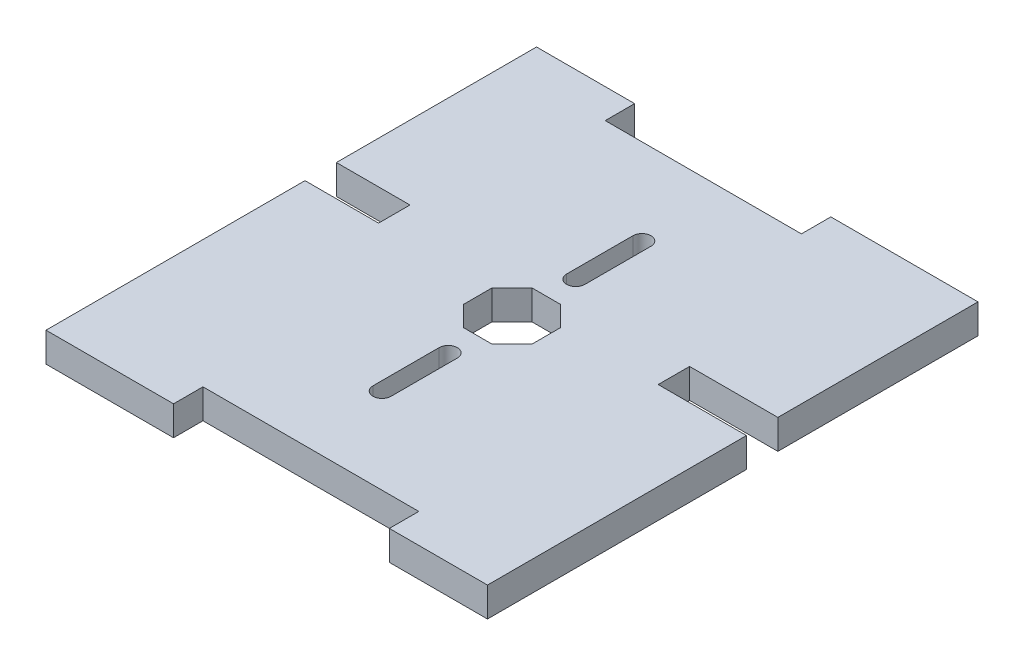
SolidWorks part; units mm, degrees
ref_plane "Front Plane" through (0, 0, 0) normal (0, 0, 1) x (1, 0, 0)
ref_plane "Top Plane" through (0, 0, 0) normal (0, 1, 0) x (1, 0, 0)
ref_plane "Right Plane" through (0, 0, 0) normal (1, 0, 0) x (0, 0, -1)
sketch "Sketch1" plane through (0, 0, 0) normal (0, 1, 0) x (1, 0, 0)
  line L1 (0, 0) -> (45, 0)
  line L2 (0, 0) -> (0, 50)
  line L3 (0, 50) -> (45, 50)
  line L4 (45, 0) -> (45, 50)
  dimension "D1" = 50
  dimension "D2" = 45
extrude "Boss-Extrude1" add sketch "Sketch1" along normal blind 3
sketch "Sketch2" plane through (0, 3, 0) normal (0, 1, 0) x (1, 0, 0)
  line L0 (45, 50) -> (0, 50) construction
  line L1 (10, 50) -> (30, 50)
  line L2 (10, 50) -> (10, 47)
  line L3 (10, 47) -> (30, 47)
  line L4 (30, 50) -> (30, 47)
  line L5 (0, 50) -> (0, 0) construction
  line L6 (0, 0) -> (45, 0) construction
  line L7 (13, 0) -> (35, 0)
  line L8 (13, 0) -> (13, 3)
  line L9 (13, 3) -> (35, 3)
  line L10 (35, 0) -> (35, 3)
  line L11 (45, 0) -> (45, 50) construction
  line L12 (0, 29.5) -> (7.5, 29.5)
  line L13 (0, 29.5) -> (0, 26.5)
  line L14 (0, 26.5) -> (7.5, 26.5)
  line L15 (7.5, 29.5) -> (7.5, 26.5)
  line L16 (45, 29.5) -> (36, 29.5)
  line L17 (45, 29.5) -> (45, 26.5)
  line L18 (45, 26.5) -> (36, 26.5)
  line L19 (36, 29.5) -> (36, 26.5)
  line L20 (22.5, 31.5) -> (22.5, 38.25) construction
  line L21 (21.0503, 21.5) -> (23.9497, 21.5)
  line L22 (23.9497, 21.5) -> (26, 23.5503)
  line L23 (26, 23.5503) -> (26, 26.4497)
  line L24 (26, 26.4497) -> (23.9497, 28.5)
  line L25 (23.9497, 28.5) -> (21.0503, 28.5)
  line L26 (21.0503, 28.5) -> (19, 26.4497)
  line L27 (19, 26.4497) -> (19, 23.5503)
  line L28 (19, 23.5503) -> (21.0503, 21.5)
  line L29 (21.575, 31.5) -> (21.575, 38.25)
  line L30 (23.425, 31.5) -> (23.425, 38.25)
  line L31 (22.5, 18.5) -> (22.5, 11.75) construction
  line L32 (23.425, 18.5) -> (23.425, 11.75)
  line L33 (21.575, 18.5) -> (21.575, 11.75)
  circle A0 centre (22.5, 25) radius 3.7884 construction
  arc A1 (21.575, 31.5) -> (23.425, 31.5) centre (22.5, 31.5) ccw
  arc A2 (23.425, 38.25) -> (21.575, 38.25) centre (22.5, 38.25) ccw
  arc A3 (23.425, 18.5) -> (21.575, 18.5) centre (22.5, 18.5) ccw
  arc A4 (21.575, 11.75) -> (23.425, 11.75) centre (22.5, 11.75) ccw
  point P25 (22.5, 34.875)
  point P41 (22.5, 15.125)
  dimension "D17" = 3
  dimension "D18" = 6.75
  dimension "D1" = 20
  dimension "D2" = 10
  dimension "D3" = 3
  dimension "D4" = 22
  dimension "D5" = 3
  dimension "D6" = 13
  dimension "D7" = 7.5
  dimension "D8" = 9
  dimension "D9" = 3
  dimension "D10" = 20.5
  dimension "D11" = 18.5
  dimension "D12" = 18.5
  dimension "D13" = 19
  dimension "D14" = 19
  dimension "D15" = 1.85
  dimension "D16" = 3
extrude "Cut-Extrude1" cut sketch "Sketch2" against normal through all
sketch "Sketch3" plane through (0, 0, 0) normal (0, 0, 1) x (1, 0, 0)
  line L0 (45, 3) -> (45, 0) construction
  line L1 (0, 3) -> (45, 3)
  line L2 (0, 3) -> (0, 2.9)
  line L3 (0, 2.9) -> (45, 2.9)
  line L4 (45, 3) -> (45, 2.9)
  line L6 (0, 0) -> (45, 0)
  line L7 (0, 0) -> (0, 0.1)
  line L8 (0, 0.1) -> (45, 0.1)
  line L9 (45, 0) -> (45, 0.1)
  dimension "D1" = 0.1
ref_plane "Plane5" through (0, 0, -25) normal (0, 0, 1) x (1, 0, 0)
sketch "Sketch4" plane through (0, 3, 0) normal (0, 1, 0) x (1, 0, 0)
  line L0 (36, 29.5) -> (36, 26.5) construction
  line L1 (0, 29.5) -> (7.5, 29.5)
  line L2 (0, 29.5) -> (0, 29.6)
  line L3 (0, 29.6) -> (7.5, 29.6)
  line L4 (7.5, 29.5) -> (7.5, 29.6)
  line L5 (0, 26.5) -> (7.5, 26.5)
  line L6 (0, 26.5) -> (0, 26.4)
  line L7 (0, 26.4) -> (7.5, 26.4)
  line L8 (7.5, 26.5) -> (7.5, 26.4)
  line L9 (45, 26.5) -> (36, 26.5)
  line L10 (45, 26.5) -> (45, 26.4)
  line L11 (45, 26.4) -> (36, 26.4)
  line L12 (36, 26.5) -> (36, 26.4)
  line L13 (45, 29.5) -> (36, 29.5)
  line L14 (45, 29.5) -> (45, 29.6)
  line L15 (45, 29.6) -> (36, 29.6)
  line L16 (36, 29.5) -> (36, 29.6)
  line L17 (7.5, 26.5) -> (7.5, 29.5) construction
  dimension "D1" = 0.1
extrude "Cut-Extrude2" cut sketch "Sketch4" against normal through all
